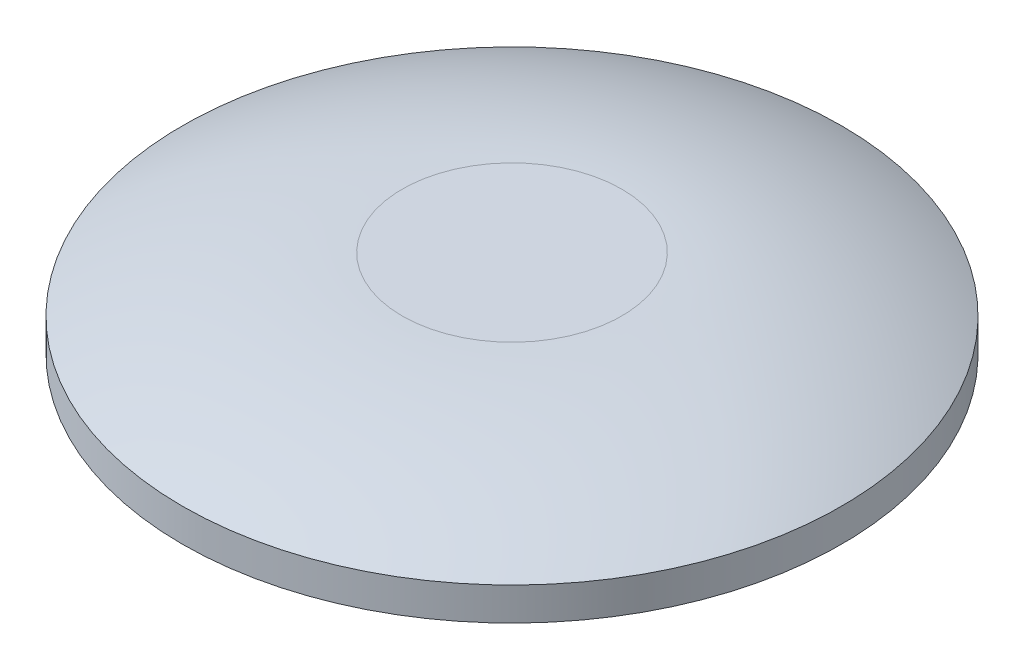
SolidWorks part; units mm, degrees
ref_plane "Front Plane" through (0, 0, 0) normal (0, 0, 1) x (1, 0, 0)
ref_plane "Top Plane" through (0, 0, 0) normal (0, 1, 0) x (1, 0, 0)
ref_plane "Right Plane" through (0, 0, 0) normal (1, 0, 0) x (0, 0, -1)
sketch "Sketch1" plane through (0, 0, 0) normal (0, 0, 1) x (1, 0, 0)
  line L0 (0, 0) -> (0, 5) construction
  line L1 (0, 0) -> (10, 0)
  line L2 (10, 0) -> (10, 1)
  line L3 (10, 1) -> (15, 1)
  line L4 (15, 1) -> (15, 2.5)
  line L5 (0, 0) -> (0, 5)
  line L6 (0, 5) -> (0, 6.1511) construction
  line L7 (0, 5) -> (5, 5)
  arc A0 (5, 5) -> (15, 2.5) centre (5, -16.25) cw
  dimension "D1" = 20
  dimension "D2" = 30
  dimension "D3" = 1
  dimension "D4" = 1.5
  dimension "D5" = 5
  dimension "D6" = 10
revolve "Revolve1" add sketch "Sketch1" angle 360 about L0
